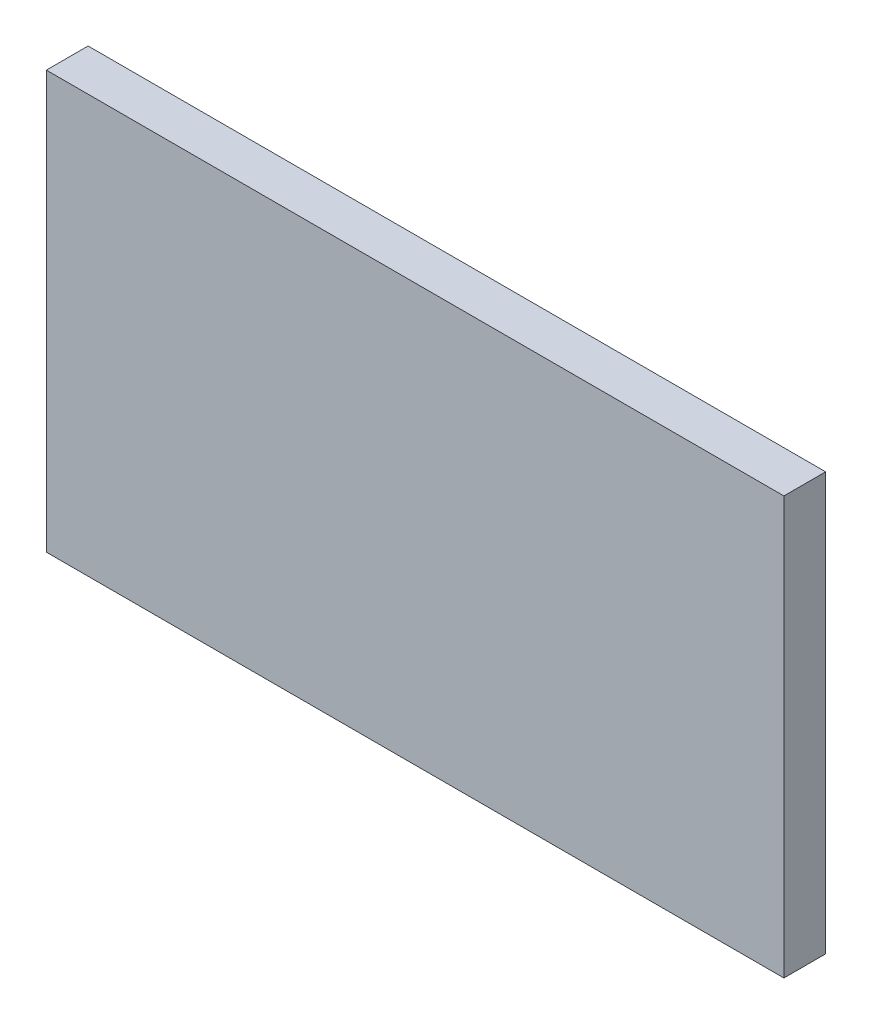
SolidWorks part; units mm, degrees
ref_plane "Plan de face" through (0, 0, 0) normal (0, 0, 1) x (1, 0, 0)
ref_plane "Plan de dessus" through (0, 0, 0) normal (0, 1, 0) x (1, 0, 0)
ref_plane "Plan de droite" through (0, 0, 0) normal (1, 0, 0) x (0, 0, -1)
sketch "Esquisse1" plane through (0, 0, 0) normal (0, 0, 1) x (1, 0, 0)
  line L1 (-68.2173, 35.8199) -> (-15.2173, 35.8199)
  line L2 (-68.2173, 35.8199) -> (-68.2173, 5.8199)
  line L3 (-68.2173, 5.8199) -> (-15.2173, 5.8199)
  line L4 (-15.2173, 35.8199) -> (-15.2173, 5.8199)
  dimension "D1" = 53
  dimension "D2" = 30
extrude "Boss.-Extru.1" add sketch "Esquisse1" along normal blind 3
equation "\"EpaisseurPlaque\"= 3"
equation "\"ProfondeurBoite\"=460"
equation "\"LongueurSyphon\"=270"
equation "\"LargeurSyphon\"=120"
equation "\"HauteurCoteDroit\"= 490"
equation "\"HauteurCoteGauche\"= 540"
equation "\"HauteurSolSyphon\"= 300"
equation "\"HauteurSyphon\"=\"HauteurCoteGauche\"-\"HauteurSolSyphon\""
equation "\"LargeurDroite\"=10"
equation "\"LargeurGauche\"=150"
equation "\"LargeurBoite\"= \"LargeurDroite\" + \"LargeurGauche\" + \"LargeurSyphon\""
equation "\"HauteurBagueSyphon\"=50"
